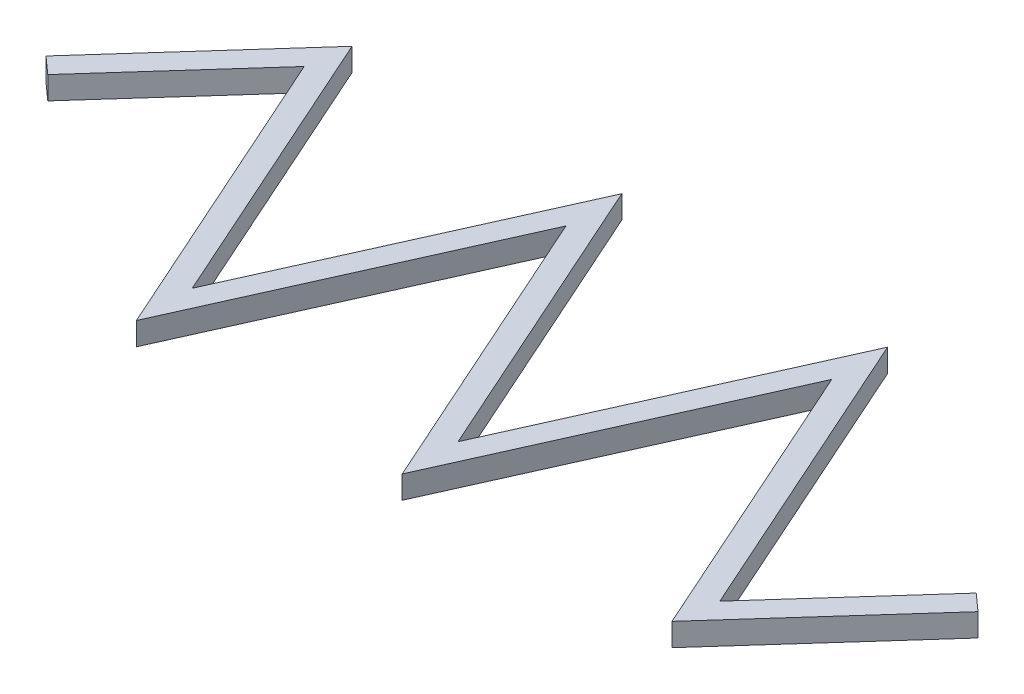
SolidWorks part; units mm, degrees
other "DetailItem1"
ref_plane "Front" through (0, 0, 0) normal (0, 0, 1) x (1, 0, 0)
ref_plane "Top" through (0, 0, 0) normal (0, 1, 0) x (1, 0, 0)
ref_plane "Right" through (0, 0, 0) normal (1, 0, 0) x (0, 0, -1)
sketch "Sketch1" plane through (0, 0, 0) normal (0, 1, 0) x (1, 0, 0)
  line L0 (-93.1775, 0) -> (0, 0) construction
  line L1 (-93.1775, 0) -> (0, 0) construction
  line L2 (0, 0) -> (-46.5887, 0) construction
  line L3 (-46.5887, 0) -> (-23.2944, 0) construction
  line L4 (-23.2944, 0) -> (-34.9416, 0) construction
  line L5 (-34.9416, 0) -> (-23.2944, 0) construction
  line L6 (-23.2944, 0) -> (0, 0) construction
  line L7 (-23.2944, 0) -> (-11.6472, 0) construction
  line L8 (-11.6472, 0) -> (-46.5887, 0) construction
  line L9 (-46.5887, 0) -> (-93.1775, 0) construction
  line L10 (-93.1775, 0) -> (-69.8831, 0) construction
  line L11 (-69.8831, 0) -> (-81.5303, 0) construction
  line L12 (-81.5303, 0) -> (-69.8831, 0) construction
  line L13 (-69.8831, 0) -> (-46.5887, 0) construction
  line L14 (-46.5887, 0) -> (-58.2359, 0) construction
  line L15 (-81.5303, 0) -> (-81.5303, 13) construction
  line L16 (-69.8831, 0) -> (-69.8831, -13) construction
  line L17 (-58.2359, 0) -> (-58.2359, 13) construction
  line L18 (-46.5887, 0) -> (-46.5887, -13) construction
  line L19 (-34.9416, 0) -> (-34.9416, 13) construction
  line L20 (-23.2944, 0) -> (-23.2944, -13) construction
  line L21 (-11.6472, 0) -> (-11.6472, 30.931) construction
  line L22 (-93.1775, 0) -> (-81.5303, 13)
  line L23 (-81.5303, 13) -> (-69.8831, -13)
  line L24 (-69.8831, -13) -> (-58.2359, 13)
  line L25 (-58.2359, 13) -> (-46.5887, -13)
  line L26 (-46.5887, -13) -> (-34.9416, 13)
  line L27 (-34.9416, 13) -> (-23.2944, -13)
  line L28 (-23.2944, -13) -> (-11.6472, 0)
  line L29 (-93.9223, 0.6673) -> (-81.2473, 14.8144)
  line L30 (-81.2473, 14.8144) -> (-69.8831, -10.554)
  line L31 (-69.8831, -10.554) -> (-58.2359, 15.446)
  line L32 (-58.2359, 15.446) -> (-46.5887, -10.554)
  line L33 (-46.5887, -10.554) -> (-34.9416, 15.446)
  line L34 (-34.9416, 15.446) -> (-23.0114, -11.1856)
  line L35 (-23.0114, -11.1856) -> (-12.392, 0.6673)
  line L36 (-92.4327, -0.6673) -> (-81.8133, 11.1856)
  line L37 (-81.8133, 11.1856) -> (-69.8831, -15.446)
  line L38 (-69.8831, -15.446) -> (-58.2359, 10.554)
  line L39 (-58.2359, 10.554) -> (-46.5887, -15.446)
  line L40 (-46.5887, -15.446) -> (-34.9416, 10.554)
  line L41 (-34.9416, 10.554) -> (-23.5773, -14.8144)
  line L42 (-23.5773, -14.8144) -> (-10.9024, -0.6673)
  line L43 (-93.9223, 0.6673) -> (-92.4327, -0.6673)
  line L44 (-12.392, 0.6673) -> (-10.9024, -0.6673)
  dimension "D1" = 13
  dimension "D2" = 13
  dimension "D3" = 1
  dimension "D4" = 1
extrude "Boss-Extrude1" add sketch "Sketch1" along normal blind 2 contours L44 L35 L34 L33 L32 L31 L30 L29 L43 L22 L23 L24 L25 L26 L27 L28 | L44 L28 L27 L26 L25 L24 L23 L22 L43 L36 L37 L38 L39 L40 L41 L42
